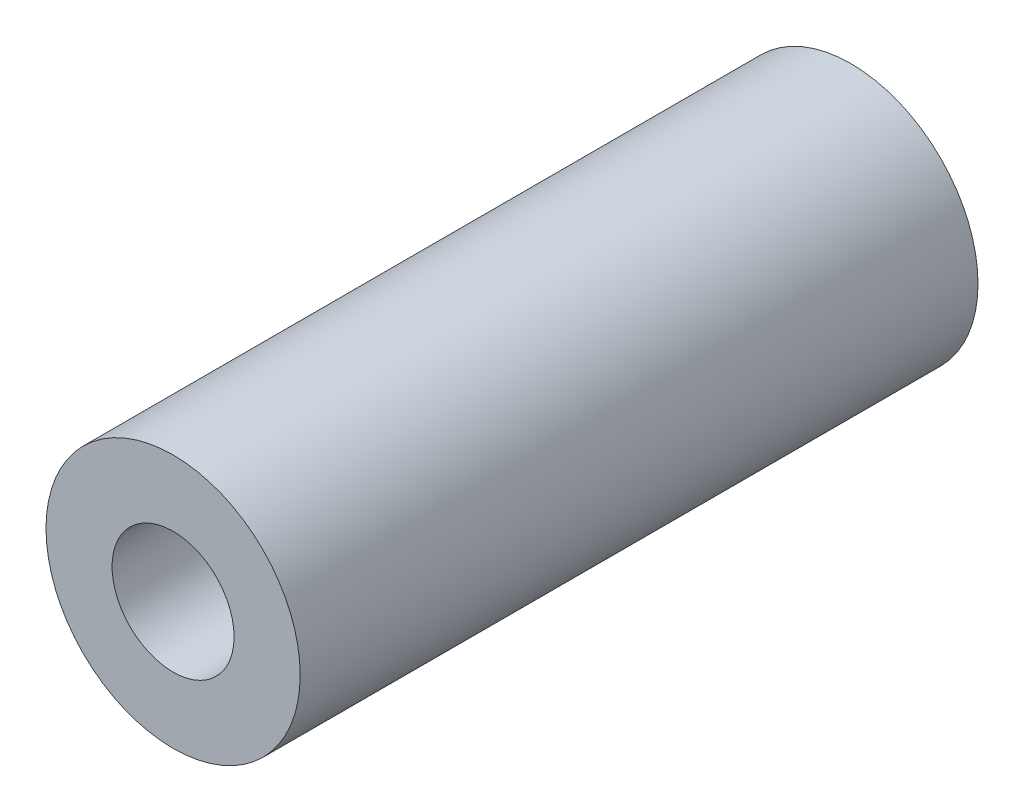
SolidWorks part; units mm, degrees
ref_plane "Front Plane" through (0, 0, 0) normal (0, 0, 1) x (1, 0, 0)
ref_plane "Top Plane" through (0, 0, 0) normal (0, 1, 0) x (1, 0, 0)
ref_plane "Right Plane" through (0, 0, 0) normal (1, 0, 0) x (0, 0, -1)
sketch "Sketch1" plane through (0, 0, 0) normal (0, 0, 1) x (1, 0, 0)
  circle A0 centre (0, 0) radius 2.3813
  circle A1 centre (0, 0) radius 1.143
  dimension "OD" = 4.7625
  dimension "ID" = 2.286
extrude "Extrude1" add sketch "Sketch1" along normal mid plane 12.7
sketch "Sketch2" plane through (0, 0, 0) normal (1, 0, 0) x (0, 0, -1)
  line L0 (-6.35, -1.143) -> (6.35, -1.143) construction
  line L3 (6.35, 1.143) -> (-6.35, 1.143) construction
  line L5 (-6.35, -1.143) -> (6.35, -1.143)
  line L6 (6.35, 1.143) -> (-6.35, 1.143)
sketch "Sketch4" plane through (0, 0, 6.35) normal (0, 0, 1) x (1, 0, 0)
  line L0 (0, 0) -> (-0.8082, 0.8082)
  line L1 (0, -1.7463) -> (0, 1.7463) construction
  circle A0 centre (0, 0) radius 1.143 construction
  dimension "D1" = 45
